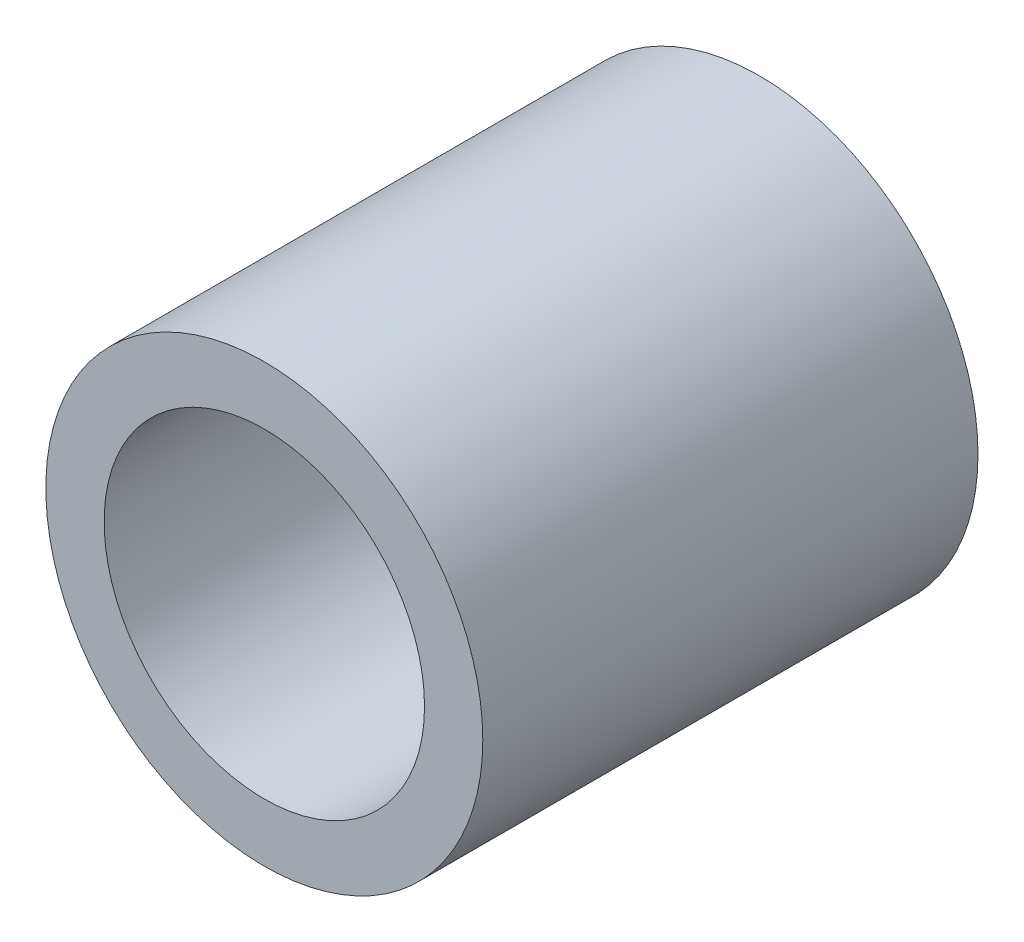
SolidWorks part; units mm, degrees
ref_plane "Front Plane" through (0, 0, 0) normal (0, 0, 1) x (1, 0, 0)
ref_plane "Top Plane" through (0, 0, 0) normal (0, 1, 0) x (1, 0, 0)
ref_plane "Right Plane" through (0, 0, 0) normal (1, 0, 0) x (0, 0, -1)
sketch "Sketch1" plane through (0, 0, 0) normal (0, 0, 1) x (1, 0, 0)
  circle A0 centre (0, 0) radius 15.24
  circle A1 centre (0, 0) radius 11.176
  dimension "D1" = 30.48
  dimension "D2" = 4.064
extrude "Boss-Extrude1" add sketch "Sketch1" along normal blind 34.544
